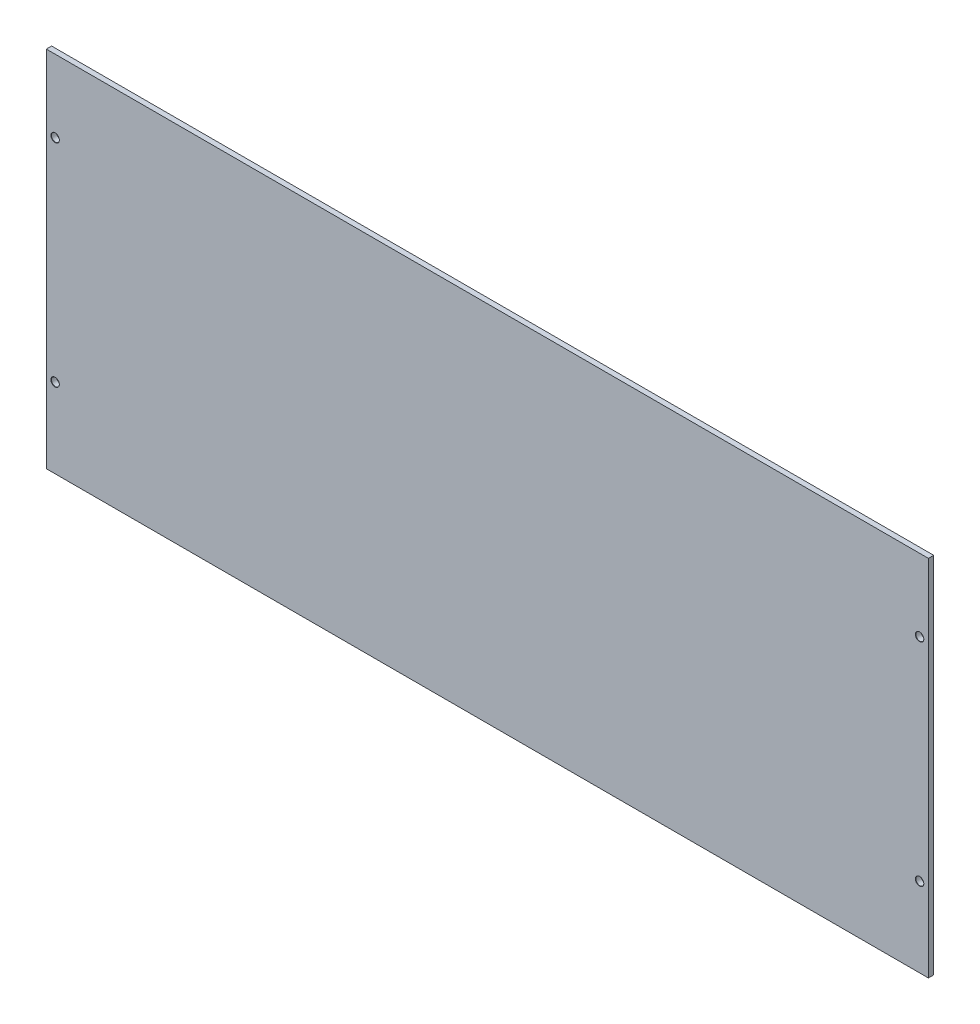
SolidWorks part; units mm, degrees
ref_plane "Спереди" through (0, 0, 0) normal (0, 0, 1) x (1, 0, 0)
ref_plane "Сверху" through (0, 0, 0) normal (0, 1, 0) x (1, 0, 0)
ref_plane "Справа" through (0, 0, 0) normal (1, 0, 0) x (0, 0, -1)
sketch "Эскиз1" plane through (0, 0, 0) normal (0, 0, 1) x (1, 0, 0)
  line L1 (0, 0) -> (500, 0)
  line L2 (0, 0) -> (0, 206)
  line L3 (0, 206) -> (500, 206)
  line L4 (500, 0) -> (500, 206)
  dimension "D1" = 500
  dimension "D2" = 206
extrude "Бобышка-Вытянуть1" add sketch "Эскиз1" along normal blind 3
hole_wizard "Отверстие с зазором M41" positions "Эскиз3" profile "Эскиз2" hole size "M4" standard "Ansi (метрические)"
sketch "Эскиз3" plane through (0, 0, 3) normal (0, 0, 1) x (1, 0, 0)
  line L0 (0, 206) -> (0, 0) construction
  line L1 (0, 0) -> (500, 0) construction
  point P0 (5, 165)
  point P1 (5, 45)
  point P3 (495, 45)
  point P5 (495, 165)
  dimension "D1" = 490
  dimension "D2" = 120
  dimension "D3" = 5
  dimension "D4" = 45
sketch "Эскиз2" plane through (5, 165, 3) normal (1, 0, 0) x (0, -1, 0)
  line L0 (0, 0) -> (0, 11.3519)
  line L1 (0, 11.3519) -> (2.25, 10)
  line L2 (2.25, 10) -> (2.25, 0.15)
  line L3 (2.25, 0.15) -> (2.4, 0)
  line L5 (2.4, 0) -> (0, 0)
  line L6 (-2.25, 0.15) -> (-2.4, 0) construction
  line L10 (0, 11.3519) -> (-2.25, 10) construction
  line L11 (0, -6.35) -> (0, 107.95) construction
  dimension "Диаметр отверстия" = 4.5
  dimension "Глубина отверстия" = 10
  dimension "Диаметр передней зенковки" = 4.8
  dimension "Угол передней зенковки" = 90
  dimension "Угол заточки сверла" = 118
